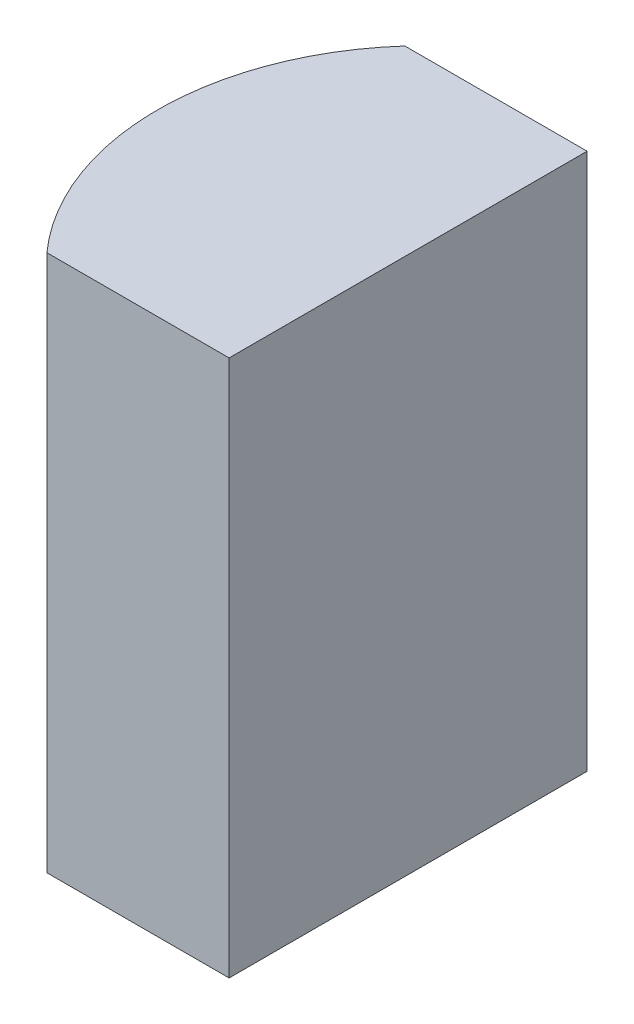
SolidWorks part; units mm, degrees
ref_plane "前视基准面" through (0, 0, 0) normal (0, 0, 1) x (1, 0, 0)
ref_plane "上视基准面" through (0, 0, 0) normal (0, 1, 0) x (1, 0, 0)
ref_plane "右视基准面" through (0, 0, 0) normal (1, 0, 0) x (0, 0, -1)
sketch "草图1" plane through (0, 0, 0) normal (0, 1, 0) x (1, 0, 0)
  line L0 (0, 0) -> (0, -4)
  line L1 (0, 0) -> (-2.0361, 0)
  line L2 (0, -4) -> (-2.0361, -4)
  line L3 (0, -2) -> (6.7931, -2) construction
  arc A0 (-2.0361, 0) -> (-2.0361, -4) centre (0.2, -2) ccw
  point P7 (-2.8, -2)
  dimension "D2" = 3
  dimension "D3" = 2.8
  dimension "D1" = 4
extrude "凸台-拉伸1" add sketch "草图1" along normal blind 6
